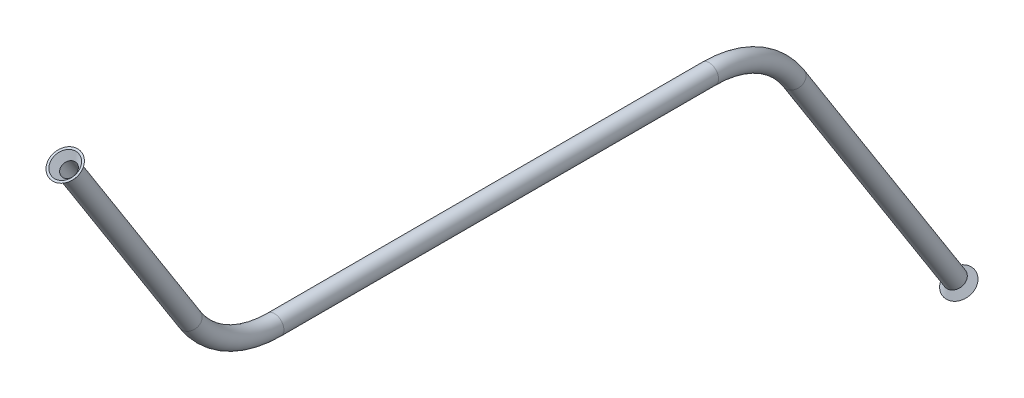
SolidWorks part; units mm, degrees
ref_plane "Front Plane" through (0, 0, 0) normal (0, 0, 1) x (1, 0, 0)
ref_plane "Top Plane" through (0, 0, 0) normal (0, 1, 0) x (1, 0, 0)
ref_plane "Right Plane" through (0, 0, 0) normal (1, 0, 0) x (0, 0, -1)
sketch "Sketch1" plane through (0, 0, 0) normal (0, 0, 1) x (1, 0, 0)
  circle A0 centre (0, 0) radius 2.3812
  circle A1 centre (0, 0) radius 1.8224
  dimension "D1" = 0.5588
  dimension "D2" = 4.7625
sketch "Sketch2" plane through (0, 0, 0) normal (1, 0, 0) x (0, 0, -1)
  line L0 (0, 0) -> (110.1307, 0)
  line L1 (131.5703, -11.78) -> (172.4302, -76.0988)
  line L2 (122.3621, -3.139) -> (36.6037, -57.6189) construction
  line L3 (36.6037, -57.6189) -> (0, 0) construction
  arc A0 (110.1307, 0) -> (131.5703, -11.78) centre (110.1307, -25.4) cw
  dimension "D3" = 25.4
  dimension "D1" = 68.2625
  dimension "D2" = 101.6
  dimension "D4" = 76.2
sweep "Sweep2" add profiles "Sketch1" path "Sketch2"
sketch "Sketch3" plane through (0, 0, 0) normal (1, 0, 0) x (0, 0, -1)
  line L0 (-21.4396, 11.78) -> (-52.0846, 60.0191)
  line L1 (131.5703, -11.78) -> (172.4302, -76.0988) construction
  line L2 (110.1307, 0) -> (0, 0) construction
  arc A0 (0, 0) -> (-21.4396, 11.78) centre (0, 25.4) cw
  dimension "D1" = 25.4
  dimension "D2" = 57.15
sketch "Sketch4" plane through (0, 0, 0) normal (0, 0, 1) x (1, 0, 0)
  circle A0 centre (0, 0) radius 2.3812 construction
  circle A1 centre (0, 0) radius 1.8224 construction
  circle A2 centre (0, 0) radius 2.3812
  circle A3 centre (0, 0) radius 1.8225
sweep "Sweep3" add profiles "Sketch4" path "Sketch3"
sketch "Sketch5" plane through (0, 66.3358, 42.1413) normal (0, 0.8441, 0.5362) x (1, 0, 0)
  circle A0 centre (0, -11.78) radius 2.3812 construction
  circle A1 centre (0, -11.78) radius 2.3813
extrude "Boss-Extrude1" add sketch "Sketch5" along normal blind 1.778 draft 37 draft outward yes
sketch "Sketch6" plane through (0, 66.3358, 42.1413) normal (0, -0.8441, -0.5362) x (1, 0, 0)
  circle A0 centre (0, 11.78) radius 1.8225 construction
  circle A1 centre (0, 11.78) radius 1.8225
extrude "Cut-Extrude1" cut sketch "Sketch6" against normal through all draft 37 draft outward yes
sketch "Sketch7" plane through (0, -132.2619, -84.0224) normal (0, -0.8441, -0.5362) x (1, 0, 0)
  circle A0 centre (0, -104.739) radius 2.3812 construction
  circle A1 centre (0, -104.739) radius 2.3812
extrude "Boss-Extrude2" add sketch "Sketch7" along normal blind 1.778 draft 37 draft outward yes
sketch "Sketch8" plane through (0, -132.2619, -84.0224) normal (0, 0.8441, 0.5362) x (1, 0, 0)
  circle A0 centre (0, 104.739) radius 1.8224 construction
  circle A1 centre (0, 104.739) radius 1.8225
extrude "Cut-Extrude2" cut sketch "Sketch8" against normal through all draft 37 draft outward yes
